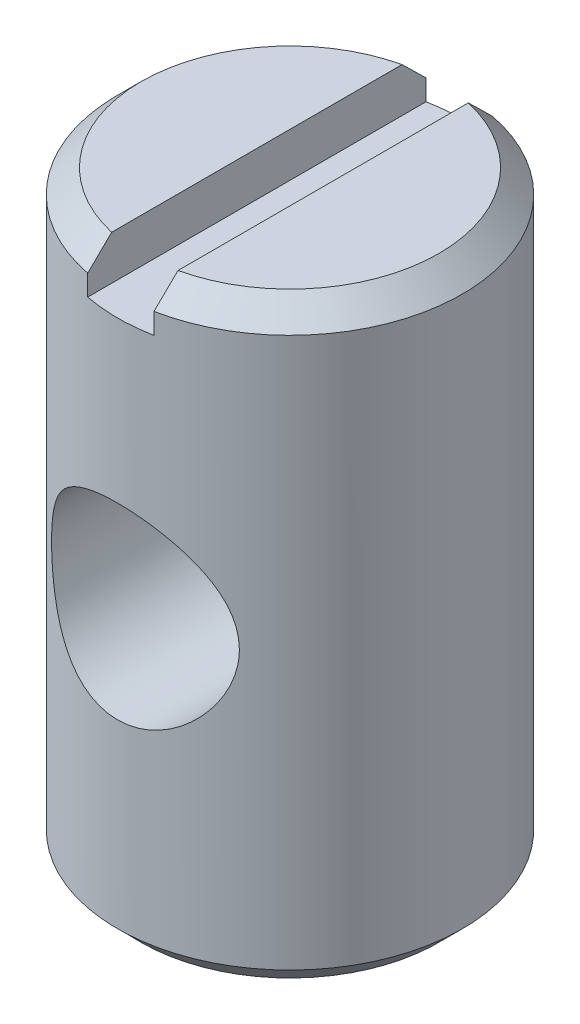
SolidWorks part; units mm, degrees
material "1060 Alloy"
ref_plane "Front Plane" through (0, 0, 0) normal (0, 0, 1) x (1, 0, 0)
ref_plane "Top Plane" through (0, 0, 0) normal (0, 1, 0) x (1, 0, 0)
ref_plane "Right Plane" through (0, 0, 0) normal (1, 0, 0) x (0, 0, -1)
sketch "Sketch3" plane through (0, 0, 0) normal (0, 0, 1) x (1, 0, 0)
  line L0 (3.4236, 13.716) -> (3.9624, 13.1772)
  line L1 (0, 0) -> (3.4236, 0)
  line L2 (0, 0) -> (0, 13.716)
  line L3 (0, 13.716) -> (3.4236, 13.716)
  line L4 (3.9624, 0.5388) -> (3.9624, 13.1772)
  line L5 (3.4236, 0) -> (3.9624, 0.5388)
  line L6 (0, 6.858) -> (3.9624, 6.858) construction
  dimension "D1" = 3.9624
  dimension "D2" = 45
  dimension "D3" = 13.716
  dimension "D4" = 0.762
  dimension "D5" = 45
  dimension "D6" = 0.762
revolve "Revolve1" add sketch "Sketch3" angle 360 about L2
sketch "Sketch4" plane through (0, 13.716, 0) normal (0, 1, 0) x (1, 0, 0)
  line L1 (-0.762, 4.4214) -> (0.762, 4.4214)
  line L2 (-0.762, 4.4214) -> (-0.762, -4.6184)
  line L3 (-0.762, -4.6184) -> (0.762, -4.6184)
  line L4 (0.762, 4.4214) -> (0.762, -4.6184)
  point P4 (0, 4.4214)
  dimension "D1" = 1.524
extrude "Cut-Extrude2" cut sketch "Sketch4" against normal blind 1.016
sketch "Sketch9" plane through (0, 0, 0) normal (0, 0, 1) x (1, 0, 0)
  circle A0 centre (0, 6.858) radius 2.159
  dimension "D1" = 4.318
extrude "Cut-Extrude3" cut sketch "Sketch9" against normal through all both and the other way through all
